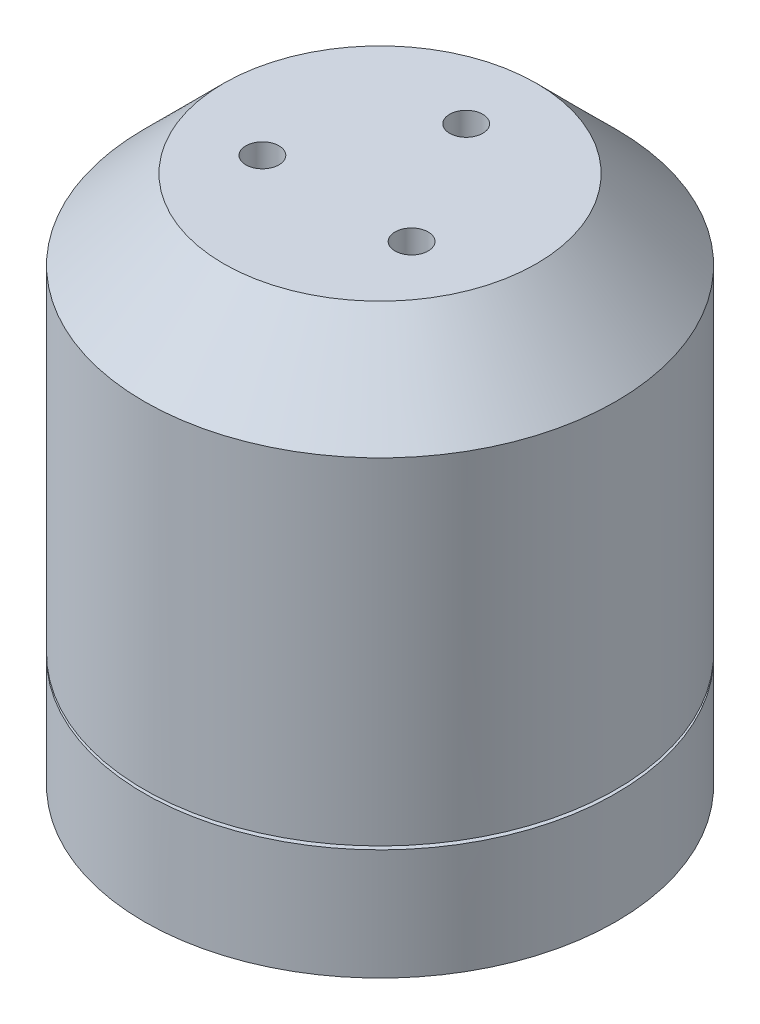
SolidWorks part; units mm, degrees
ref_plane "Front Plane" through (0, 0, 0) normal (0, 0, 1) x (1, 0, 0)
ref_plane "Top Plane" through (0, 0, 0) normal (0, 1, 0) x (1, 0, 0)
ref_plane "Right Plane" through (0, 0, 0) normal (1, 0, 0) x (0, 0, -1)
other "Bounding Box"
ref_plane "Default Plane" through (13.8565, 3.175, 6.7999) normal (0, -1, 0) x (-1, 0, 0)
sketch "Sketch1" plane through (0, 0, 0) normal (0, 1, 0) x (1, 0, 0)
  circle A0 centre (0, 0) radius 17.8
  dimension "D1" = 35.6
extrude "Boss-Extrude1" add sketch "Sketch1" along normal mid plane 40
sketch "Sketch2" plane through (0, 20, 0) normal (0, 1, 0) x (1, 0, 0)
  line L0 (0, 0) -> (0, 6.5) construction
  circle A0 centre (0, 6.5) radius 1.25
  circle A1 centre (0, 0) radius 6.5 construction
  dimension "D1" = 2.5
  dimension "D2" = 13
extrude "Cut-Extrude1" cut sketch "Sketch2" against normal blind 12.7
pattern_circular "CirPattern1" count 3 over 360 about axis through (0, 0, 0) along (0, 1, 0) of "Cut-Extrude1"
sketch "Sketch3" plane through (0, -20, 0) normal (0, -1, 0) x (1, 0, 0)
  line L0 (0, 0) -> (0, 12.5) construction
  circle A0 centre (0, 12.5) radius 1.5
  dimension "D2" = 3
  dimension "D1" = 12.5
extrude "Cut-Extrude2" cut sketch "Sketch3" against normal blind 12.7
pattern_circular "CirPattern2" count 4 over 360 about axis through (0, 0, 0) along (0, 1, 0) of "Cut-Extrude2"
chamfer "Chamfer1" distance 6 angle 45 1 edges at (0, 20, 17.8)
sketch "Sketch4" plane through (0, -20, 0) normal (0, -1, 0) x (1, 0, 0)
  circle A0 centre (0, 0) radius 17.8
  circle A1 centre (0, 0) radius 17.8 construction
  circle A2 centre (0, 0) radius 2.5
  dimension "D1" = 5
extrude "Cut-Extrude3" cut sketch "Sketch4" against normal blind 0.254 from offset 8.382 offset against normal yes
